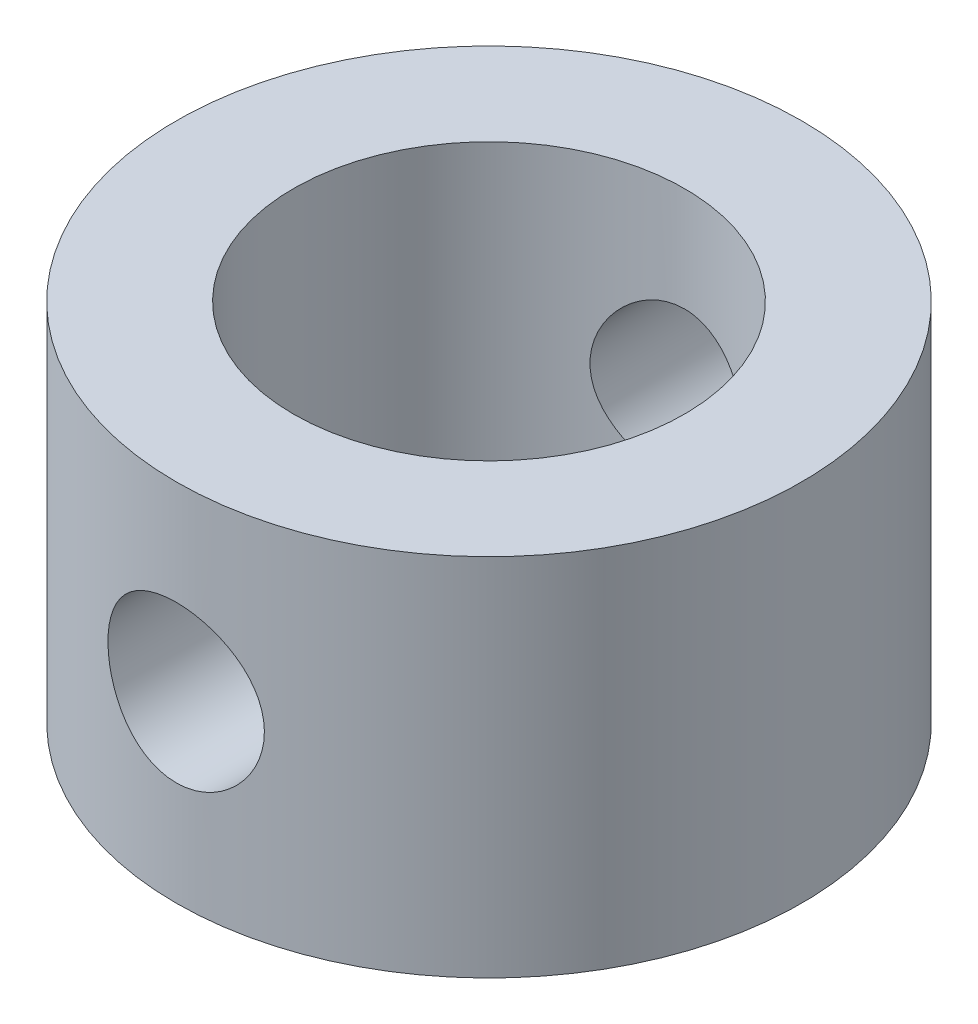
SolidWorks part; units mm, degrees
ref_plane "Front Plane" through (0, 0, 0) normal (0, 0, 1) x (1, 0, 0)
ref_plane "Top Plane" through (0, 0, 0) normal (0, 1, 0) x (1, 0, 0)
ref_plane "Right Plane" through (0, 0, 0) normal (1, 0, 0) x (0, 0, -1)
sketch "Sketch1" plane through (0, 0, 0) normal (0, 1, 0) x (1, 0, 0)
  circle A0 centre (0, 0) radius 7.5
  circle A1 centre (0, 0) radius 12
  dimension "D1" = 24
  dimension "D2" = 15
extrude "Boss-Extrude1" add sketch "Sketch1" along normal mid plane 14
sketch "Sketch2" plane through (0, 0, 0) normal (0, 0, 1) x (1, 0, 0)
  circle A0 centre (0, 0) radius 3
  dimension "D1" = 6
extrude "Cut-Extrude1" cut sketch "Sketch2" against normal through all both and the other way through all
